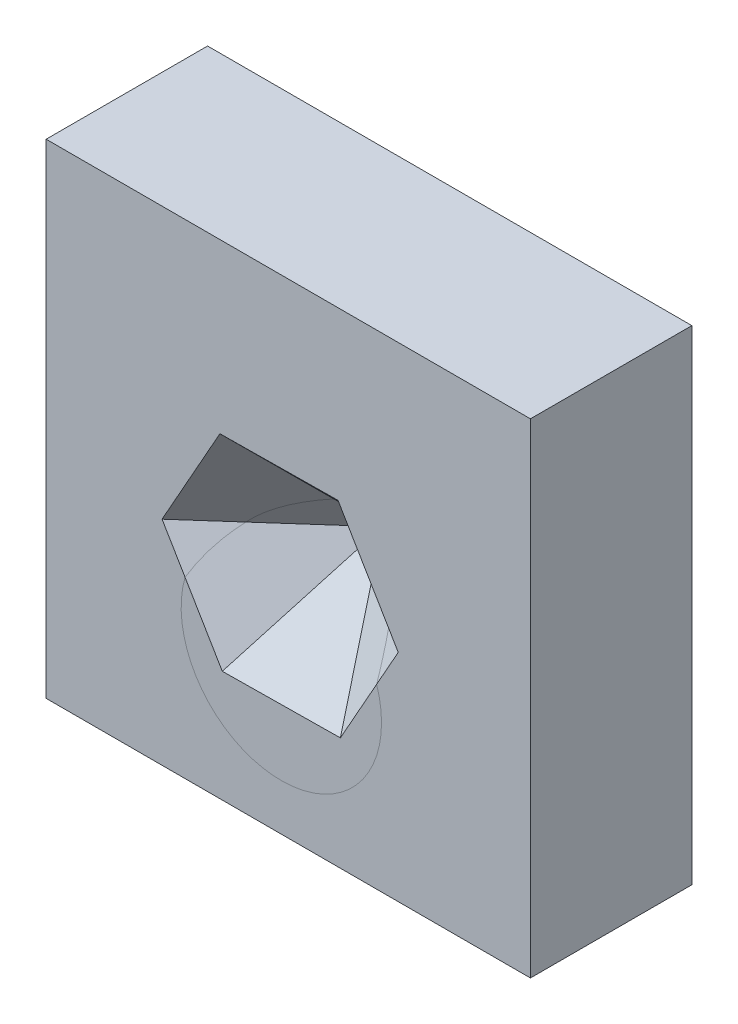
SolidWorks part; units mm, degrees
material "7075-T6, Plate (SS)"
ref_plane "Ebene vorne" through (0, 0, 0) normal (0, 0, 1) x (1, 0, 0)
ref_plane "Ebene oben" through (0, 0, 0) normal (0, 1, 0) x (1, 0, 0)
ref_plane "Ebene rechts" through (0, 0, 0) normal (1, 0, 0) x (0, 0, -1)
sketch "Skizze3" plane through (0, 0, 0) normal (0, 0, 1) x (1, 0, 0)
  line L1 (0, 0) -> (150, 0)
  line L2 (0, 0) -> (0, -150)
  line L3 (0, -150) -> (150, -150)
  line L4 (150, 0) -> (150, -150)
  dimension "D1" = 150
extrude "Aufsatz-Linear austragen1" add sketch "Skizze3" against normal blind 50
sketch "Skizze4" plane through (0, 0, 0) normal (0, 0, 1) x (1, 0, 0)
  line L1 (90.3995, -51.6628) -> (53.8218, -52.0874)
  line L2 (53.8218, -52.0874) -> (35.9006, -83.977)
  line L3 (35.9006, -83.977) -> (54.5572, -115.442)
  line L4 (54.5572, -115.442) -> (91.135, -115.0174)
  line L5 (91.135, -115.0174) -> (109.0561, -83.1278)
  line L6 (109.0561, -83.1278) -> (90.3995, -51.6628)
  circle A0 centre (72.4784, -83.5524) radius 31.6794 construction
extrude "Schnitt-Linear austragen1" cut sketch "Skizze4" against normal blind 41 draft 45
ref_plane "Ebene1" through (0, 0, 50) normal (0, 0, 1) x (1, 0, 0)
sketch "Skizze5" plane through (0, 0, 50) normal (0, 0, 1) x (1, 0, 0)
  circle A0 centre (72.8461, -104.5979) radius 31.0321
  point P2 (72.8461, -104.5979)
split line "Trennlinie2"
equation "\"LÄNGE\"=0"
equation "\"BREITE\"=0"
equation "\"HÖHE\"=0"
equation "\"DURCHMESSER\"=0"
equation "\"Stückzahl\"= 1"
equation "\"W_ID\"= 0000"
